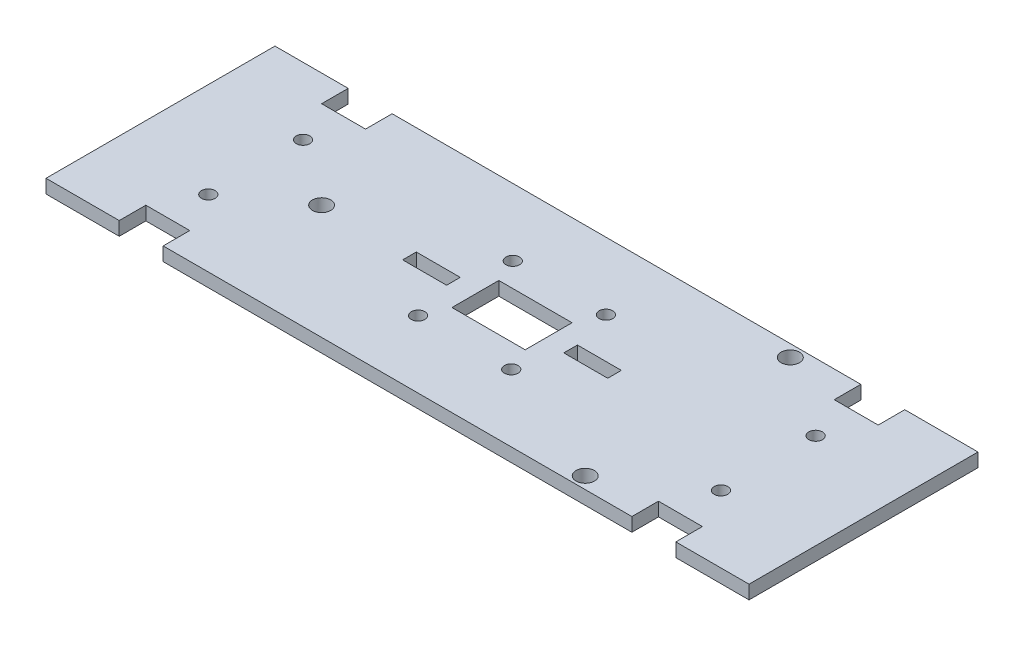
SolidWorks part; units mm, degrees
ref_plane "Front Plane" through (0, 0, 0) normal (0, 0, 1) x (1, 0, 0)
ref_plane "Top Plane" through (0, 0, 0) normal (0, 1, 0) x (1, 0, 0)
ref_plane "Right Plane" through (0, 0, 0) normal (1, 0, 0) x (0, 0, -1)
sketch "Sketch2" plane through (0, 0, 0) normal (0, 1, 0) x (1, 0, 0)
  line L0 (0, 6.6321) -> (0, -7.2626) construction
  line L1 (-76.2, 24.8158) -> (-60.325, 24.8158)
  line L2 (-76.2, 24.8158) -> (-76.2, -24.8158)
  line L3 (-76.2, -24.8158) -> (-60.325, -24.8158)
  line L4 (76.2, 24.8158) -> (76.2, -24.8158)
  line L5 (-76.2, 24.8158) -> (76.2, -24.8158) construction
  line L6 (-76.2, -24.8158) -> (76.2, 24.8158) construction
  line L7 (-22.225, 1.4796) -> (-12.7, 1.4796)
  line L8 (-22.225, 1.4796) -> (-22.225, -1.4795)
  line L9 (-22.225, -1.4795) -> (-12.7, -1.4795)
  line L10 (-12.7, 1.4796) -> (-12.7, -1.4795)
  line L11 (-22.225, 1.4796) -> (-12.7, -1.4795) construction
  line L12 (-22.225, -1.4795) -> (-12.7, 1.4796) construction
  line L13 (-6.6624, 0) -> (7.9449, 0) construction
  line L14 (22.225, -1.4795) -> (12.7, 1.4796) construction
  line L15 (22.225, 1.4796) -> (12.7, -1.4795) construction
  line L16 (12.7, 1.4796) -> (12.7, -1.4795)
  line L17 (22.225, -1.4795) -> (12.7, -1.4795)
  line L18 (22.225, 1.4796) -> (22.225, -1.4795)
  line L19 (22.225, 1.4796) -> (12.7, 1.4796)
  line L20 (60.325, 24.8158) -> (76.2, 24.8158)
  line L21 (-60.325, 24.8158) -> (-60.325, 19.05)
  line L22 (-60.325, 19.05) -> (-50.8, 19.05)
  line L23 (-50.8, 24.8158) -> (-50.8, 19.05)
  line L24 (-60.325, 24.8158) -> (-50.8, 19.05) construction
  line L25 (-60.325, 19.05) -> (-50.8, 24.8158) construction
  line L26 (60.325, 19.05) -> (50.8, 24.8158) construction
  line L27 (60.325, 24.8158) -> (50.8, 19.05) construction
  line L28 (50.8, 24.8158) -> (50.8, 19.05)
  line L29 (60.325, 19.05) -> (50.8, 19.05)
  line L30 (60.325, 24.8158) -> (60.325, 19.05)
  line L31 (60.325, -24.8158) -> (76.2, -24.8158)
  line L32 (60.325, -24.8158) -> (50.8, -19.05) construction
  line L33 (60.325, -19.05) -> (50.8, -24.8158) construction
  line L34 (-60.325, -19.05) -> (-50.8, -24.8158) construction
  line L35 (-60.325, -24.8158) -> (-50.8, -19.05) construction
  line L36 (-50.8, -24.8158) -> (50.8, -24.8158)
  line L37 (60.325, -24.8158) -> (60.325, -19.05)
  line L38 (60.325, -19.05) -> (50.8, -19.05)
  line L39 (50.8, -24.8158) -> (50.8, -19.05)
  line L40 (-50.8, -24.8158) -> (-50.8, -19.05)
  line L41 (-60.325, -19.05) -> (-50.8, -19.05)
  line L42 (-60.325, -24.8158) -> (-60.325, -19.05)
  line L44 (-50.8, 24.8158) -> (50.8, 24.8158)
  line L45 (-7.9375, 5.08) -> (7.9375, 5.08)
  line L46 (-7.9375, 5.08) -> (-7.9375, -5.08)
  line L47 (-7.9375, -5.08) -> (7.9375, -5.08)
  line L48 (7.9375, 5.08) -> (7.9375, -5.08)
  line L49 (-7.9375, 5.08) -> (7.9375, -5.08) construction
  line L50 (-7.9375, -5.08) -> (7.9375, 5.08) construction
  point P0 (0, 0)
  point P6 (-17.4625, 0)
  point P19 (17.4625, 0)
  point P20 (-55.5625, 21.9329)
  point P29 (55.5625, 21.9329)
  point P38 (55.5625, -21.9329)
  point P39 (-55.5625, -21.9329)
  point P40 (0, 0)
  dimension "D1" = 38.1
  dimension "D2" = 152.4
  dimension "D3" = 2.9591
  dimension "D4" = 9.525
  dimension "D5" = 44.45
  dimension "D6" = 5.7658
  dimension "D7" = 9.525
  dimension "D8" = 10.16
  dimension "D9" = 15.875
  dimension "D10" = 101.6
extrude "Boss-Extrude1" add sketch "Sketch2" along normal blind 2.9591
hole_wizard "#4 Clearance Hole1" positions "Sketch4" profile "Sketch3" hole size "#4" standard "ANSI Inch"
sketch "Sketch4" plane through (0, 2.9591, 0) normal (0, 1, 0) x (1, 0, 0)
  line L2 (-10.0965, -10.2648) -> (10.0965, -10.2648)
  line L3 (-10.0965, -10.2648) -> (-10.0965, 10.2648)
  line L4 (-10.0965, 10.2648) -> (10.0965, 10.2648)
  line L5 (10.0965, -10.2648) -> (10.0965, 10.2648)
  line L6 (-10.0965, -10.2648) -> (10.0965, 10.2648) construction
  line L7 (-10.0965, 10.2648) -> (10.0965, -10.2648) construction
  line L11 (-12.7, 1.4796) -> (-22.225, 1.4796) construction
  line L12 (-13.7795, 1.4796) -> (-13.7795, 10.2648)
  line L14 (-17.4625, 1.4796) -> (-17.4625, 19.05)
  line L16 (-55.5625, -10.2648) -> (55.5625, -10.2648)
  line L17 (-55.5625, -10.2648) -> (-55.5625, 10.2648)
  line L18 (-55.5625, 10.2648) -> (55.5625, 10.2648)
  line L19 (55.5625, -10.2648) -> (55.5625, 10.2648)
  line L20 (-55.5625, -10.2648) -> (55.5625, 10.2648) construction
  line L21 (-55.5625, 10.2648) -> (55.5625, -10.2648) construction
  line L22 (-50.8, 19.05) -> (-60.325, 19.05) construction
  circle A0 centre (-17.4625, 1.4796) radius 3.683
  circle A1 centre (-10.0965, 10.2648) radius 3.683
  point P125 (0, 0)
  point P126 (10.0965, 10.2648)
  point P251 (-10.0965, -10.2648)
  point P252 (-10.0965, 10.2648)
  point P253 (10.0965, -10.2648)
  point P296 (-17.4625, 10.2648)
  point P299 (0, 0)
  point P802 (-55.5625, 19.05)
  point P803 (55.5625, 10.2648)
  point P805 (-55.5625, -10.2648)
  point P807 (55.5625, -10.2648)
  point P809 (-55.5625, 10.2648)
  dimension "D1" = 7.366
  dimension "D2" = 7.366
  dimension "D3" = 20.5296
sketch "Sketch3" plane through (0, 2.9591, 0) normal (1, 0, 0) x (0, 0, 1)
  line L0 (0, 0) -> (0, 4.1872)
  line L1 (0, 4.1872) -> (1.4732, 3.302)
  line L2 (1.4732, 3.302) -> (1.4732, 0)
  line L5 (1.4732, 0) -> (0, 0)
  line L10 (0, 4.1872) -> (-1.4732, 3.302) construction
  line L11 (0, -6.35) -> (0, 107.95) construction
  dimension "Hole Dia." = 2.9464
  dimension "Hole Depth" = 3.302
  dimension "Drill Angle" = 118
sketch "Sketch5" plane through (0, 2.9591, 0) normal (0, 1, 0) x (1, 0, 0)
  line L1 (-46.0375, 24.8158) -> (-36.5125, 24.8158)
  line L2 (-46.0375, 24.8158) -> (-46.0375, -24.8158)
  line L3 (-46.0375, -24.8158) -> (-36.5125, -24.8158)
  line L4 (-36.5125, 24.8158) -> (-36.5125, -24.8158)
  line L5 (22.225, 0) -> (-36.5125, 0) construction
  line L6 (22.225, -1.4795) -> (22.225, 1.4796) construction
  circle A0 centre (-41.275, 0) radius 1.4732 construction
  point P7 (-41.275, 24.8158)
  point P8 (-36.5125, 0)
  dimension "D1" = 2.9464
  dimension "D2" = 9.525
  dimension "D3" = 41.275
hole_wizard "#4 Clearance Hole2" positions "Sketch7" profile "Sketch6" hole size "#4" standard "ANSI Inch"
sketch "Sketch7" plane through (0, 2.9591, 0) normal (0, 1, 0) x (1, 0, 0)
  point P0 (-41.275, 0)
sketch "Sketch6" plane through (-41.275, 2.9591, 0) normal (1, 0, 0) x (0, 0, 1)
  line L0 (0, 0) -> (0, 4.4924)
  line L1 (0, 4.4924) -> (1.9812, 3.302)
  line L2 (1.9812, 3.302) -> (1.9812, 0)
  line L5 (1.9812, 0) -> (0, 0)
  line L10 (0, 4.4924) -> (-1.9812, 3.302) construction
  line L11 (0, -6.35) -> (0, 107.95) construction
  dimension "Hole Dia." = 3.9624
  dimension "Hole Depth" = 3.302
  dimension "Drill Angle" = 118
hole_wizard "Tap Drill for #4 Helicoil1" positions "Sketch9" profile "Sketch8" hole size "#4-40" standard "ANSI Inch"
sketch "Sketch9" plane through (0, 0, 0) normal (0, -1, 0) x (-1, 0, 0)
  line L0 (-38.1, 22.225) -> (-38.1, -22.225) construction
  line L2 (-76.2, -24.8158) -> (-76.2, 24.8158) construction
  point P0 (-38.1, 22.225)
  point P2 (-38.1, -22.225)
  point P10 (-38.1, 0)
  dimension "D1" = 44.45
  dimension "D2" = 38.1
sketch "Sketch8" plane through (38.1, 0, -22.225) normal (1, 0, 0) x (0, 0, -1)
  line L0 (0, 0) -> (0, 6.7861)
  line L1 (0, 6.7861) -> (1.9939, 5.588)
  line L2 (1.9939, 5.588) -> (1.9939, 0)
  line L5 (1.9939, 0) -> (0, 0)
  line L10 (0, 6.7861) -> (-1.9939, 5.588) construction
  line L11 (0, -6.35) -> (0, 107.95) construction
  dimension "Hole Dia." = 3.9878
  dimension "Hole Depth" = 5.588
  dimension "Drill Angle" = 118
sketch "Sketch10" [suppressed] plane through (0, 0, 0) normal (0, -1, 0) x (1, 0, 0)
  circle A0 centre (-41.275, 0) radius 2.3812
  dimension "D1" = 4.7625
extrude "Cut-Extrude1" [suppressed] cut sketch "Sketch10" against normal through all
